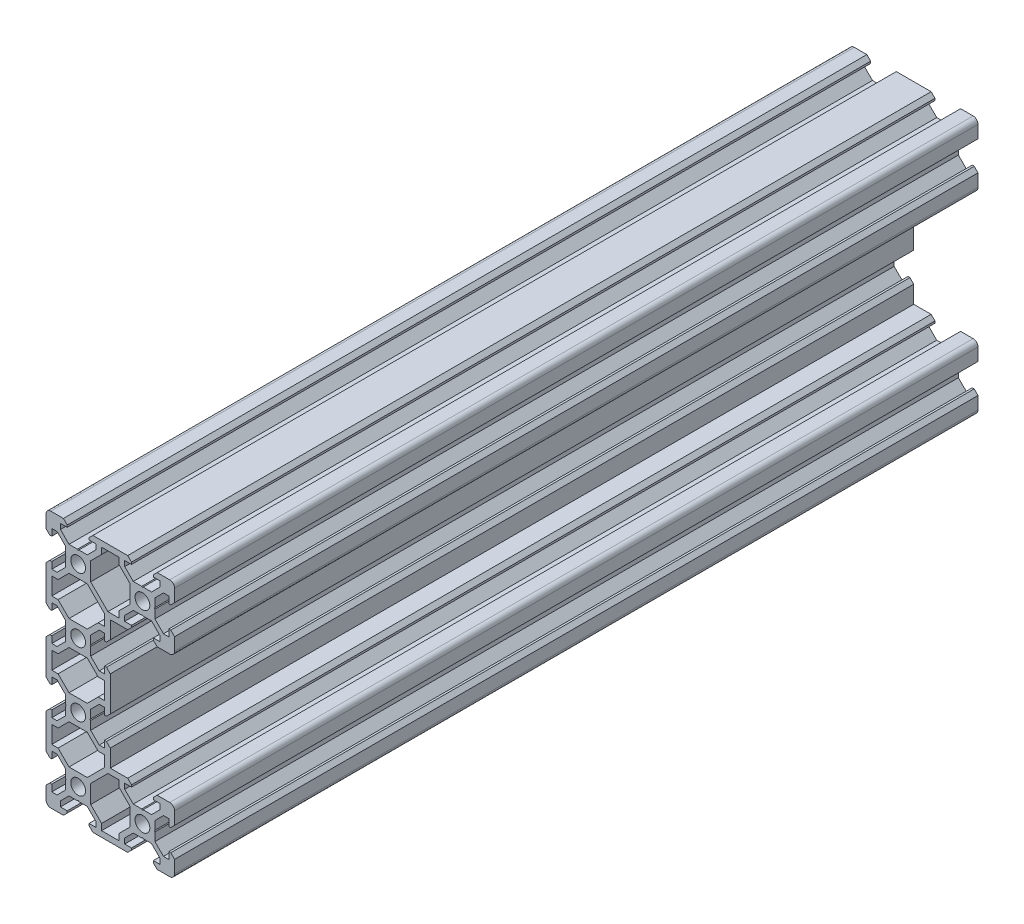
SolidWorks part; units mm, degrees
material "6061-T6 (SS)"
ref_plane "Front Plane" through (0, 0, 0) normal (0, 0, 1) x (1, 0, 0)
ref_plane "Top Plane" through (0, 0, 0) normal (0, 1, 0) x (1, 0, 0)
ref_plane "Right Plane" through (0, 0, 0) normal (1, 0, 0) x (0, 0, -1)
sketch "Sketch1" plane through (0, 0, 0) normal (0, 0, 1) x (1, 0, 0)
  line L0 (-20, -38.5) -> (-20, 38.5)
  line L1 (-18.5, 40) -> (18.5, 40)
  line L2 (20, 38.5) -> (20, 21.5)
  line L3 (18.5, 20) -> (0, 20)
  line L4 (0, 20) -> (0, -20)
  line L5 (0, 0) -> (-20, 0) construction
  line L6 (18.5, -20) -> (0, -20)
  line L7 (20, -38.5) -> (20, -21.5)
  line L8 (-18.5, -40) -> (18.5, -40)
  line L9 (20, 30) -> (10, 30) construction
  line L10 (-10, 0) -> (-10, 10) construction
  arc A0 (-18.5, -40) -> (-20, -38.5) centre (-18.5, -38.5) cw
  arc A1 (20, -38.5) -> (18.5, -40) centre (18.5, -38.5) cw
  arc A2 (18.5, -20) -> (20, -21.5) centre (18.5, -21.5) cw
  arc A3 (20, 21.5) -> (18.5, 20) centre (18.5, 21.5) cw
  arc A4 (18.5, 40) -> (20, 38.5) centre (18.5, 38.5) cw
  arc A5 (-20, 38.5) -> (-18.5, 40) centre (-18.5, 38.5) cw
  circle A6 centre (10, 30) radius 2.3
  circle A7 centre (-10, 30) radius 2.3
  circle A8 centre (-10, 10) radius 2.3
  circle A9 centre (-10, -10) radius 2.3
  circle A10 centre (10, -30) radius 2.3
  circle A11 centre (-10, -30) radius 2.3
  point P13 (-20, -40)
  point P16 (20, -40)
  point P19 (20, -20)
  point P22 (20, 20)
  point P25 (20, 40)
  point P28 (-20, 40)
  line B0 (-10, 30) -> (-10, 40) construction
  line B1 (-10, 33.69) -> (-10.21, 33.9)
  line B2 (-10.21, 33.9) -> (-12.8393, 33.9)
  line B3 (-12.8393, 33.9) -> (-15.5, 36.5607)
  line B4 (-15.5, 36.5607) -> (-15.5, 38.2)
  line B5 (-15.5, 38.2) -> (-13.395, 38.2)
  line B6 (-13.395, 38.2) -> (-13.395, 38.815)
  line B7 (-13.395, 38.815) -> (-14.58, 40)
  line B8 (-14.58, 40) -> (-5.42, 40)
  line B9 (-10, 30) -> (-15.9132, 35.9132) construction
  line B10 (-6.605, 38.815) -> (-5.42, 40)
  line B11 (-6.605, 38.2) -> (-6.605, 38.815)
  line B12 (-4.5, 38.2) -> (-6.605, 38.2)
  line B13 (-4.5, 36.5607) -> (-4.5, 38.2)
  line B14 (-7.1607, 33.9) -> (-4.5, 36.5607)
  line B15 (-9.79, 33.9) -> (-7.1607, 33.9)
  line B16 (-10, 33.69) -> (-9.79, 33.9)
  line B17 (10, 30) -> (10, 40) construction
  line B18 (10, 33.69) -> (9.79, 33.9)
  line B19 (9.79, 33.9) -> (7.1607, 33.9)
  line B20 (7.1607, 33.9) -> (4.5, 36.5607)
  line B21 (4.5, 36.5607) -> (4.5, 38.2)
  line B22 (4.5, 38.2) -> (6.605, 38.2)
  line B23 (6.605, 38.2) -> (6.605, 38.815)
  line B24 (6.605, 38.815) -> (5.42, 40)
  line B25 (5.42, 40) -> (14.58, 40)
  line B26 (10, 30) -> (4.0868, 35.9132) construction
  line B27 (13.395, 38.815) -> (14.58, 40)
  line B28 (13.395, 38.2) -> (13.395, 38.815)
  line B29 (15.5, 38.2) -> (13.395, 38.2)
  line B30 (15.5, 36.5607) -> (15.5, 38.2)
  line B31 (12.8393, 33.9) -> (15.5, 36.5607)
  line B32 (10.21, 33.9) -> (12.8393, 33.9)
  line B33 (10, 33.69) -> (10.21, 33.9)
  line B34 (10, -30) -> (10, -20) construction
  line B35 (10, -26.31) -> (9.79, -26.1)
  line B36 (9.79, -26.1) -> (7.1607, -26.1)
  line B37 (7.1607, -26.1) -> (4.5, -23.4393)
  line B38 (4.5, -23.4393) -> (4.5, -21.8)
  line B39 (4.5, -21.8) -> (6.605, -21.8)
  line B40 (6.605, -21.8) -> (6.605, -21.185)
  line B41 (6.605, -21.185) -> (5.42, -20)
  line B42 (5.42, -20) -> (14.58, -20)
  line B43 (10, -30) -> (4.0868, -24.0868) construction
  line B44 (13.395, -21.185) -> (14.58, -20)
  line B45 (13.395, -21.8) -> (13.395, -21.185)
  line B46 (15.5, -21.8) -> (13.395, -21.8)
  line B47 (15.5, -23.4393) -> (15.5, -21.8)
  line B48 (12.8393, -26.1) -> (15.5, -23.4393)
  line B49 (10.21, -26.1) -> (12.8393, -26.1)
  line B50 (10, -26.31) -> (10.21, -26.1)
  line B51 (-10, 30) -> (-20, 30) construction
  line B52 (-13.69, 30) -> (-13.9, 29.79)
  line B53 (-13.9, 29.79) -> (-13.9, 27.1607)
  line B54 (-13.9, 27.1607) -> (-16.5607, 24.5)
  line B55 (-16.5607, 24.5) -> (-18.2, 24.5)
  line B56 (-18.2, 24.5) -> (-18.2, 26.605)
  line B57 (-18.2, 26.605) -> (-18.815, 26.605)
  line B58 (-18.815, 26.605) -> (-20, 25.42)
  line B59 (-20, 25.42) -> (-20, 34.58)
  line B60 (-10, 30) -> (-15.9132, 24.0868) construction
  line B61 (-18.815, 33.395) -> (-20, 34.58)
  line B62 (-18.2, 33.395) -> (-18.815, 33.395)
  line B63 (-18.2, 35.5) -> (-18.2, 33.395)
  line B64 (-16.5607, 35.5) -> (-18.2, 35.5)
  line B65 (-13.9, 32.8393) -> (-16.5607, 35.5)
  line B66 (-13.9, 30.21) -> (-13.9, 32.8393)
  line B67 (-13.69, 30) -> (-13.9, 30.21)
  line B68 (-10, 10) -> (-20, 10) construction
  line B69 (-13.69, 10) -> (-13.9, 9.79)
  line B70 (-13.9, 9.79) -> (-13.9, 7.1607)
  line B71 (-13.9, 7.1607) -> (-16.5607, 4.5)
  line B72 (-16.5607, 4.5) -> (-18.2, 4.5)
  line B73 (-18.2, 4.5) -> (-18.2, 6.605)
  line B74 (-18.2, 6.605) -> (-18.815, 6.605)
  line B75 (-18.815, 6.605) -> (-20, 5.42)
  line B76 (-20, 5.42) -> (-20, 14.58)
  line B77 (-10, 10) -> (-15.9132, 4.0868) construction
  line B78 (-18.815, 13.395) -> (-20, 14.58)
  line B79 (-18.2, 13.395) -> (-18.815, 13.395)
  line B80 (-18.2, 15.5) -> (-18.2, 13.395)
  line B81 (-16.5607, 15.5) -> (-18.2, 15.5)
  line B82 (-13.9, 12.8393) -> (-16.5607, 15.5)
  line B83 (-13.9, 10.21) -> (-13.9, 12.8393)
  line B84 (-13.69, 10) -> (-13.9, 10.21)
  line B85 (-10, -10) -> (-20, -10) construction
  line B86 (-13.69, -10) -> (-13.9, -10.21)
  line B87 (-13.9, -10.21) -> (-13.9, -12.8393)
  line B88 (-13.9, -12.8393) -> (-16.5607, -15.5)
  line B89 (-16.5607, -15.5) -> (-18.2, -15.5)
  line B90 (-18.2, -15.5) -> (-18.2, -13.395)
  line B91 (-18.2, -13.395) -> (-18.815, -13.395)
  line B92 (-18.815, -13.395) -> (-20, -14.58)
  line B93 (-20, -14.58) -> (-20, -5.42)
  line B94 (-10, -10) -> (-15.9132, -15.9132) construction
  line B95 (-18.815, -6.605) -> (-20, -5.42)
  line B96 (-18.2, -6.605) -> (-18.815, -6.605)
  line B97 (-18.2, -4.5) -> (-18.2, -6.605)
  line B98 (-16.5607, -4.5) -> (-18.2, -4.5)
  line B99 (-13.9, -7.1607) -> (-16.5607, -4.5)
  line B100 (-13.9, -9.79) -> (-13.9, -7.1607)
  line B101 (-13.69, -10) -> (-13.9, -9.79)
  line B102 (-10, -30) -> (-20, -30) construction
  line B103 (-13.69, -30) -> (-13.9, -30.21)
  line B104 (-13.9, -30.21) -> (-13.9, -32.8393)
  line B105 (-13.9, -32.8393) -> (-16.5607, -35.5)
  line B106 (-16.5607, -35.5) -> (-18.2, -35.5)
  line B107 (-18.2, -35.5) -> (-18.2, -33.395)
  line B108 (-18.2, -33.395) -> (-18.815, -33.395)
  line B109 (-18.815, -33.395) -> (-20, -34.58)
  line B110 (-20, -34.58) -> (-20, -25.42)
  line B111 (-10, -30) -> (-15.9132, -35.9132) construction
  line B112 (-18.815, -26.605) -> (-20, -25.42)
  line B113 (-18.2, -26.605) -> (-18.815, -26.605)
  line B114 (-18.2, -24.5) -> (-18.2, -26.605)
  line B115 (-16.5607, -24.5) -> (-18.2, -24.5)
  line B116 (-13.9, -27.1607) -> (-16.5607, -24.5)
  line B117 (-13.9, -29.79) -> (-13.9, -27.1607)
  line B118 (-13.69, -30) -> (-13.9, -29.79)
  line B119 (-10, -30) -> (-10, -40) construction
  line B120 (-10, -33.69) -> (-9.79, -33.9)
  line B121 (-9.79, -33.9) -> (-7.1607, -33.9)
  line B122 (-7.1607, -33.9) -> (-4.5, -36.5607)
  line B123 (-4.5, -36.5607) -> (-4.5, -38.2)
  line B124 (-4.5, -38.2) -> (-6.605, -38.2)
  line B125 (-6.605, -38.2) -> (-6.605, -38.815)
  line B126 (-6.605, -38.815) -> (-5.42, -40)
  line B127 (-5.42, -40) -> (-14.58, -40)
  line B128 (-10, -30) -> (-4.0868, -35.9132) construction
  line B129 (-13.395, -38.815) -> (-14.58, -40)
  line B130 (-13.395, -38.2) -> (-13.395, -38.815)
  line B131 (-15.5, -38.2) -> (-13.395, -38.2)
  line B132 (-15.5, -36.5607) -> (-15.5, -38.2)
  line B133 (-12.8393, -33.9) -> (-15.5, -36.5607)
  line B134 (-10.21, -33.9) -> (-12.8393, -33.9)
  line B135 (-10, -33.69) -> (-10.21, -33.9)
  line B136 (10, -30) -> (10, -40) construction
  line B137 (10, -33.69) -> (10.21, -33.9)
  line B138 (10.21, -33.9) -> (12.8393, -33.9)
  line B139 (12.8393, -33.9) -> (15.5, -36.5607)
  line B140 (15.5, -36.5607) -> (15.5, -38.2)
  line B141 (15.5, -38.2) -> (13.395, -38.2)
  line B142 (13.395, -38.2) -> (13.395, -38.815)
  line B143 (13.395, -38.815) -> (14.58, -40)
  line B144 (14.58, -40) -> (5.42, -40)
  line B145 (10, -30) -> (15.9132, -35.9132) construction
  line B146 (6.605, -38.815) -> (5.42, -40)
  line B147 (6.605, -38.2) -> (6.605, -38.815)
  line B148 (4.5, -38.2) -> (6.605, -38.2)
  line B149 (4.5, -36.5607) -> (4.5, -38.2)
  line B150 (7.1607, -33.9) -> (4.5, -36.5607)
  line B151 (9.79, -33.9) -> (7.1607, -33.9)
  line B152 (10, -33.69) -> (9.79, -33.9)
  line B153 (10, 30) -> (10, 20) construction
  line B154 (10, 26.31) -> (10.21, 26.1)
  line B155 (10.21, 26.1) -> (12.8393, 26.1)
  line B156 (12.8393, 26.1) -> (15.5, 23.4393)
  line B157 (15.5, 23.4393) -> (15.5, 21.8)
  line B158 (15.5, 21.8) -> (13.395, 21.8)
  line B159 (13.395, 21.8) -> (13.395, 21.185)
  line B160 (13.395, 21.185) -> (14.58, 20)
  line B161 (14.58, 20) -> (5.42, 20)
  line B162 (10, 30) -> (15.9132, 24.0868) construction
  line B163 (6.605, 21.185) -> (5.42, 20)
  line B164 (6.605, 21.8) -> (6.605, 21.185)
  line B165 (4.5, 21.8) -> (6.605, 21.8)
  line B166 (4.5, 23.4393) -> (4.5, 21.8)
  line B167 (7.1607, 26.1) -> (4.5, 23.4393)
  line B168 (9.79, 26.1) -> (7.1607, 26.1)
  line B169 (10, 26.31) -> (9.79, 26.1)
  line B170 (-10, 10) -> (0, 10) construction
  line B171 (-6.31, 10) -> (-6.1, 10.21)
  line B172 (-6.1, 10.21) -> (-6.1, 12.8393)
  line B173 (-6.1, 12.8393) -> (-3.4393, 15.5)
  line B174 (-3.4393, 15.5) -> (-1.8, 15.5)
  line B175 (-1.8, 15.5) -> (-1.8, 13.395)
  line B176 (-1.8, 13.395) -> (-1.185, 13.395)
  line B177 (-1.185, 13.395) -> (0, 14.58)
  line B178 (0, 14.58) -> (0, 5.42)
  line B179 (-10, 10) -> (-4.0868, 15.9132) construction
  line B180 (-1.185, 6.605) -> (0, 5.42)
  line B181 (-1.8, 6.605) -> (-1.185, 6.605)
  line B182 (-1.8, 4.5) -> (-1.8, 6.605)
  line B183 (-3.4393, 4.5) -> (-1.8, 4.5)
  line B184 (-6.1, 7.1607) -> (-3.4393, 4.5)
  line B185 (-6.1, 9.79) -> (-6.1, 7.1607)
  line B186 (-6.31, 10) -> (-6.1, 9.79)
  line B187 (-10, -10) -> (0, -10) construction
  line B188 (-6.31, -10) -> (-6.1, -9.79)
  line B189 (-6.1, -9.79) -> (-6.1, -7.1607)
  line B190 (-6.1, -7.1607) -> (-3.4393, -4.5)
  line B191 (-3.4393, -4.5) -> (-1.8, -4.5)
  line B192 (-1.8, -4.5) -> (-1.8, -6.605)
  line B193 (-1.8, -6.605) -> (-1.185, -6.605)
  line B194 (-1.185, -6.605) -> (0, -5.42)
  line B195 (0, -5.42) -> (0, -14.58)
  line B196 (-10, -10) -> (-4.0868, -4.0868) construction
  line B197 (-1.185, -13.395) -> (0, -14.58)
  line B198 (-1.8, -13.395) -> (-1.185, -13.395)
  line B199 (-1.8, -15.5) -> (-1.8, -13.395)
  line B200 (-3.4393, -15.5) -> (-1.8, -15.5)
  line B201 (-6.1, -12.8393) -> (-3.4393, -15.5)
  line B202 (-6.1, -10.21) -> (-6.1, -12.8393)
  line B203 (-6.31, -10) -> (-6.1, -10.21)
  line B204 (10, -30) -> (20, -30) construction
  line B205 (13.69, -30) -> (13.9, -29.79)
  line B206 (13.9, -29.79) -> (13.9, -27.1607)
  line B207 (13.9, -27.1607) -> (16.5607, -24.5)
  line B208 (16.5607, -24.5) -> (18.2, -24.5)
  line B209 (18.2, -24.5) -> (18.2, -26.605)
  line B210 (18.2, -26.605) -> (18.815, -26.605)
  line B211 (18.815, -26.605) -> (20, -25.42)
  line B212 (20, -25.42) -> (20, -34.58)
  line B213 (10, -30) -> (15.9132, -24.0868) construction
  line B214 (18.815, -33.395) -> (20, -34.58)
  line B215 (18.2, -33.395) -> (18.815, -33.395)
  line B216 (18.2, -35.5) -> (18.2, -33.395)
  line B217 (16.5607, -35.5) -> (18.2, -35.5)
  line B218 (13.9, -32.8393) -> (16.5607, -35.5)
  line B219 (13.9, -30.21) -> (13.9, -32.8393)
  line B220 (13.69, -30) -> (13.9, -30.21)
  line B221 (10, 30) -> (20, 30) construction
  line B222 (13.69, 30) -> (13.9, 30.21)
  line B223 (13.9, 30.21) -> (13.9, 32.8393)
  line B224 (13.9, 32.8393) -> (16.5607, 35.5)
  line B225 (16.5607, 35.5) -> (18.2, 35.5)
  line B226 (18.2, 35.5) -> (18.2, 33.395)
  line B227 (18.2, 33.395) -> (18.815, 33.395)
  line B228 (18.815, 33.395) -> (20, 34.58)
  line B229 (20, 34.58) -> (20, 25.42)
  line B230 (10, 30) -> (15.9132, 35.9132) construction
  line B231 (18.815, 26.605) -> (20, 25.42)
  line B232 (18.2, 26.605) -> (18.815, 26.605)
  line B233 (18.2, 24.5) -> (18.2, 26.605)
  line B234 (16.5607, 24.5) -> (18.2, 24.5)
  line B235 (13.9, 27.1607) -> (16.5607, 24.5)
  line B236 (13.9, 29.79) -> (13.9, 27.1607)
  line B237 (13.69, 30) -> (13.9, 29.79)
  line B238 (-18.2, -2.7) -> (-18.2, 2.7)
  line B239 (-18.2, 2.7) -> (-16.2393, 2.7)
  line B240 (-16.2393, 2.7) -> (-12.8393, 6.1)
  line B241 (-12.8393, 6.1) -> (-7.1607, 6.1)
  line B242 (-10, 6.1) -> (-10, 0) construction
  line B243 (-10, 0) -> (-18.2, 0) construction
  line B244 (-3.7607, 2.7) -> (-7.1607, 6.1)
  line B245 (-1.8, 2.7) -> (-3.7607, 2.7)
  line B246 (-1.8, -2.7) -> (-1.8, 2.7)
  line B247 (-1.8, -2.7) -> (-3.7607, -2.7)
  line B248 (-3.7607, -2.7) -> (-7.1607, -6.1)
  line B249 (-12.8393, -6.1) -> (-7.1607, -6.1)
  line B250 (-16.2393, -2.7) -> (-12.8393, -6.1)
  line B251 (-18.2, -2.7) -> (-16.2393, -2.7)
  line B252 (-10, 6.1) -> (-10, 10) construction
  line B253 (-10, 10) -> (-15.0927, 4.9073) construction
  line B254 (-18.2, 17.3) -> (-18.2, 22.7)
  line B255 (-18.2, 22.7) -> (-16.2393, 22.7)
  line B256 (-16.2393, 22.7) -> (-12.8393, 26.1)
  line B257 (-12.8393, 26.1) -> (-7.1607, 26.1)
  line B258 (-10, 26.1) -> (-10, 20) construction
  line B259 (-10, 20) -> (-18.2, 20) construction
  line B260 (-1.8, 17.3) -> (-3.7607, 17.3)
  line B261 (-3.7607, 17.3) -> (-7.1607, 13.9)
  line B262 (-12.8393, 13.9) -> (-7.1607, 13.9)
  line B263 (-16.2393, 17.3) -> (-12.8393, 13.9)
  line B264 (-18.2, 17.3) -> (-16.2393, 17.3)
  line B265 (-10, 26.1) -> (-10, 30) construction
  line B266 (-10, 30) -> (-15.0927, 24.9073) construction
  line B267 (-7.1607, 26.1) -> (-1.8, 20.7393)
  line B268 (-1.8, 17.3) -> (-1.8, 20.7393)
  line B269 (2.7, -38.2) -> (-2.7, -38.2)
  line B270 (-2.7, -38.2) -> (-2.7, -36.2393)
  line B271 (-2.7, -36.2393) -> (-6.1, -32.8393)
  line B272 (-6.1, -32.8393) -> (-6.1, -27.1607)
  line B273 (-6.1, -30) -> (0, -30) construction
  line B274 (0, -30) -> (0, -38.2) construction
  line B275 (2.7, -21.8) -> (2.7, -23.7607)
  line B276 (2.7, -23.7607) -> (6.1, -27.1607)
  line B277 (6.1, -32.8393) -> (6.1, -27.1607)
  line B278 (2.7, -36.2393) -> (6.1, -32.8393)
  line B279 (2.7, -38.2) -> (2.7, -36.2393)
  line B280 (-6.1, -30) -> (-10, -30) construction
  line B281 (-10, -30) -> (-4.9073, -35.0927) construction
  line B282 (-6.1, -27.1607) -> (-0.7393, -21.8)
  line B283 (2.7, -21.8) -> (-0.7393, -21.8)
  line B284 (-18.2, -22.7) -> (-18.2, -17.3)
  line B285 (-18.2, -17.3) -> (-16.2393, -17.3)
  line B286 (-16.2393, -17.3) -> (-12.8393, -13.9)
  line B287 (-12.8393, -13.9) -> (-7.1607, -13.9)
  line B288 (-10, -13.9) -> (-10, -20) construction
  line B289 (-10, -20) -> (-18.2, -20) construction
  line B290 (-12.8393, -26.1) -> (-7.1607, -26.1)
  line B291 (-16.2393, -22.7) -> (-12.8393, -26.1)
  line B292 (-18.2, -22.7) -> (-16.2393, -22.7)
  line B293 (-10, -13.9) -> (-10, -10) construction
  line B294 (-10, -10) -> (-15.0927, -15.0927) construction
  line B295 (-3.7607, -17.3) -> (-7.1607, -13.9)
  line B296 (-1.8, -17.3) -> (-3.7607, -17.3)
  line B297 (-1.8, -17.3) -> (-1.8, -20.7393)
  line B298 (-1.8, -20.7393) -> (-7.1607, -26.1)
  line B299 (-2.7, 38.2) -> (2.7, 38.2)
  line B300 (2.7, 38.2) -> (2.7, 36.2393)
  line B301 (2.7, 36.2393) -> (6.1, 32.8393)
  line B302 (6.1, 32.8393) -> (6.1, 27.1607)
  line B303 (6.1, 30) -> (0, 30) construction
  line B304 (0, 30) -> (0, 38.2) construction
  line B305 (-6.1, 32.8393) -> (-6.1, 27.1607)
  line B306 (-2.7, 36.2393) -> (-6.1, 32.8393)
  line B307 (-2.7, 38.2) -> (-2.7, 36.2393)
  line B308 (6.1, 30) -> (10, 30) construction
  line B309 (10, 30) -> (4.9073, 35.0927) construction
  line B310 (2.7, 23.7607) -> (6.1, 27.1607)
  line B311 (2.7, 21.8) -> (2.7, 23.7607)
  line B312 (2.7, 21.8) -> (-0.7393, 21.8)
  line B313 (-0.7393, 21.8) -> (-6.1, 27.1607)
  dimension "D3" = 1.5
  dimension "D6" = 4.6
  dimension "D7" = 20
  dimension "D8" = 20
  dimension "D1" = 40
  dimension "D2" = 80
  dimension "D4" = 20
  dimension "D5" = 20
sketch_block_instance "V Slot 2-1"
sketch_block "V Slot 2" parameters "D1"=10, "D2"=11, "D3"=4.3, "D4"=1.8, "D5"=0.21, "D6"=45, "D7"=9.16, "D8"=1.5, "D9"=6.79
sketch_block_instance "V Slot 2-2"
sketch_block_instance "V Slot 2-3"
sketch_block_instance "V Slot 2-4"
sketch_block_instance "V Slot 2-5"
sketch_block_instance "V Slot 2-6"
sketch_block_instance "V Slot 2-7"
sketch_block_instance "V Slot 2-8"
sketch_block_instance "V Slot 2-9"
sketch_block_instance "V Slot 2-10"
sketch_block_instance "V Slot 2-11"
sketch_block_instance "V Slot 2-12"
sketch_block_instance "V Slot 2-13"
sketch_block_instance "V Slot 2-14"
sketch_block_instance "Center Cutout 1-1"
sketch_block "Center Cutout 1" parameters "D1"=5.4, "D2"=12.2, "D3"=8.2, "D4"=45, "D5"=10, "D6"=1.5
sketch_block_instance "Corner Cutout 1-1"
sketch_block "Corner Cutout 1" parameters "D1"=5.4, "D2"=12.2, "D3"=8.2, "D4"=45, "D5"=10, "D6"=1.5
sketch_block_instance "Corner Cutout 1-2"
sketch_block_instance "Corner Cutout 2-1"
sketch_block "Corner Cutout 2" parameters "D1"=5.4, "D2"=12.2, "D3"=8.2, "D4"=45, "D5"=10, "D6"=1.5
sketch_block_instance "Corner Cutout 2-2"
extrude "Boss-Extrude1" add sketch "Sketch1" along normal blind 250 contours B237 B222 B223 B224 B225 B226 B227 B228 L2 A4 L1 B27 B28 B29 B30 B31 B32 B33 B18 B19 B20 B21 B22 B23 B24 B10 B11 B12 B13 B14 B15 B16 B1 B2 B3 B4 B5 B6 B7 A5 L0 B61 B62 B63 B64 B65 B66 B67 B52
